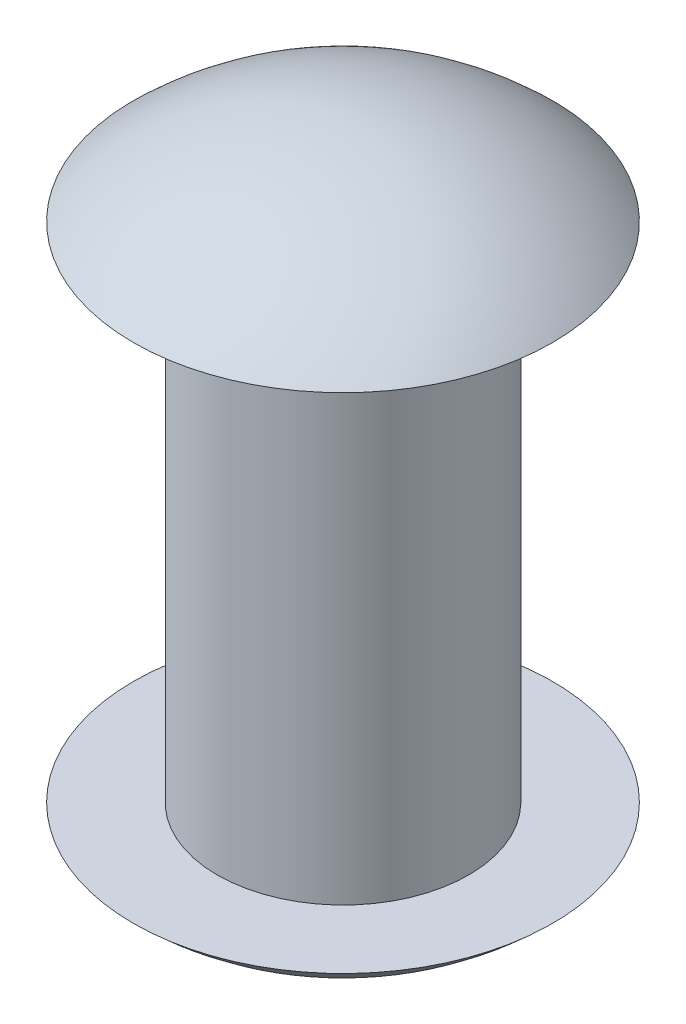
SolidWorks part; units mm, degrees
material "1023 Листовая углеродистая сталь (SS)"
ref_plane "Спереди" through (0, 0, 0) normal (0, 0, 1) x (1, 0, 0)
ref_plane "Сверху" through (0, 0, 0) normal (0, 1, 0) x (1, 0, 0)
ref_plane "Справа" through (0, 0, 0) normal (1, 0, 0) x (0, 0, -1)
sketch "Эскиз1" plane through (0, 0, 0) normal (0, 0, 1) x (1, 0, 0)
  line L0 (0, 79.6721) -> (0, -75.2459) construction
  line L1 (-23.8525, 0) -> (42.0492, 0) construction
  line L2 (15, -30) -> (15, 30)
  line L3 (15, 30) -> (25, 30)
  line L4 (0, 40) -> (-37.7948, 40) construction
  line L5 (15, -30) -> (25, -30)
  line L6 (0, 40) -> (0, -40)
  arc A0 (25, 30) -> (0, 40) centre (0, 3.75) ccw
  arc A1 (25, -30) -> (0, -40) centre (0, -3.75) cw
  point P12 (15, 0)
  dimension "D1" = 15
  dimension "D2" = 30
  dimension "D3" = 25
  dimension "D4" = 10
revolve "Повернуть1" add sketch "Эскиз1" angle 360 about L0
